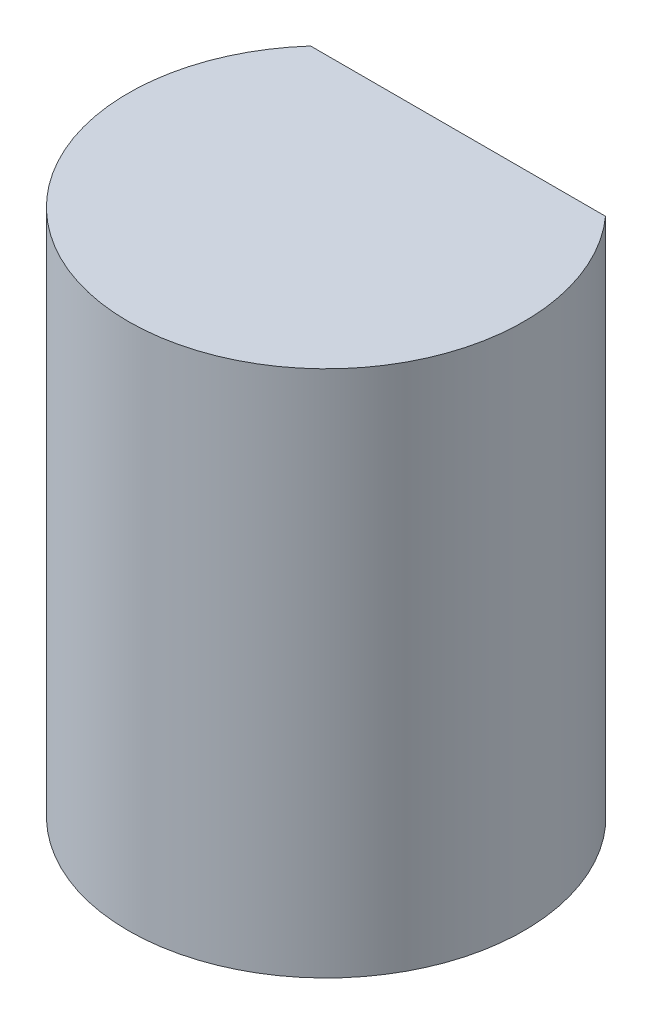
SolidWorks part; units mm, degrees
ref_plane "Front Plane" through (0, 0, 0) normal (0, 0, 1) x (1, 0, 0)
ref_plane "Top Plane" through (0, 0, 0) normal (0, 1, 0) x (1, 0, 0)
ref_plane "Right Plane" through (0, 0, 0) normal (1, 0, 0) x (0, 0, -1)
sketch "Sketch1" plane through (0, 0, 0) normal (0, 1, 0) x (1, 0, 0)
  circle A0 centre (0, 0) radius 1.5
  dimension "D1" = 3
extrude "Boss-Extrude1" add sketch "Sketch1" along normal blind 4
sketch "Sketch3" plane through (0, 4, 0) normal (0, 1, 0) x (-1, 0, 0)
  point P0 (0, 0)
sketch "Sketch4" plane through (0, 0, 0) normal (0, -1, 0) x (1, 0, 0)
  point P0 (0, 0)
sketch "Sketch6" plane through (0, 4, 0) normal (0, 1, 0) x (1, 0, 0)
  line L1 (-1.118, 1.5) -> (1.118, 1.5)
  line L2 (-1.118, 1.5) -> (-1.118, 1)
  line L3 (-1.118, 1) -> (1.118, 1)
  line L4 (1.118, 1.5) -> (1.118, 1)
  circle A0 centre (0, 0) radius 1.5 construction
  dimension "D1" = 0.5
extrude "Cut-Extrude1" cut sketch "Sketch6" against normal up to next
